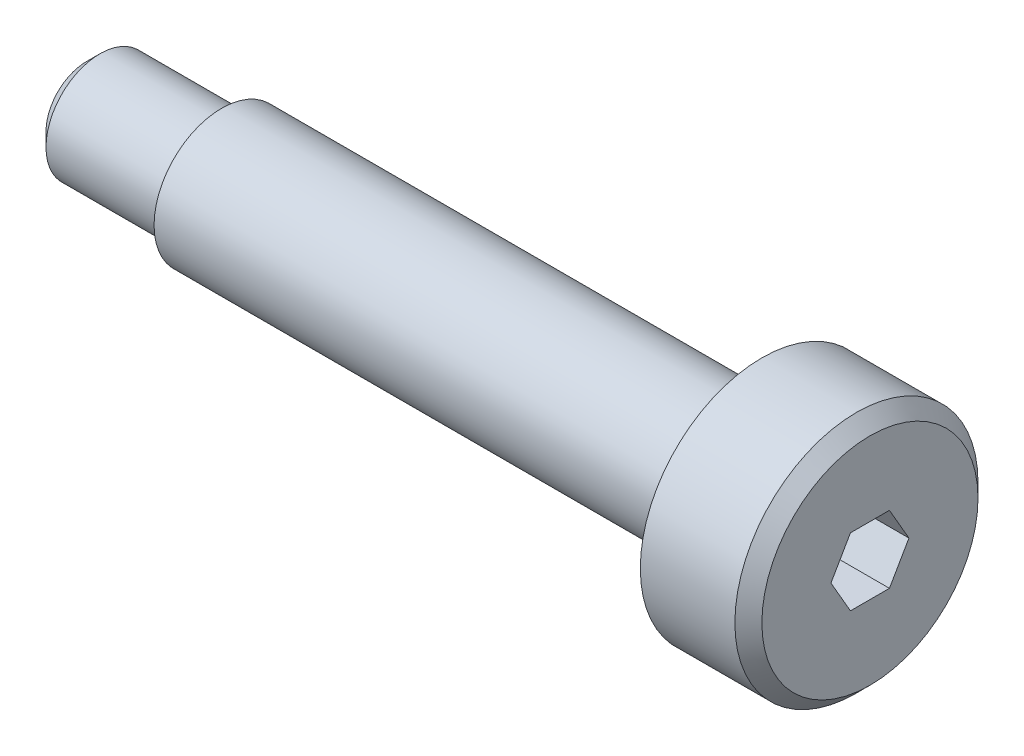
SolidWorks part; units mm, degrees
material "AISI Type 316L stainless steel"
ref_plane "Front Plane" through (0, 0, 0) normal (0, 0, 1) x (1, 0, 0)
ref_plane "Top Plane" through (0, 0, 0) normal (0, 1, 0) x (1, 0, 0)
ref_plane "Right Plane" through (0, 0, 0) normal (1, 0, 0) x (0, 0, -1)
sketch "Sketch1" plane through (0, 0, 0) normal (0, 0, 1) x (1, 0, 0)
  line L0 (0, 0) -> (29, 0)
  line L1 (29, 0) -> (29, 4)
  line L2 (28.5, 4.5) -> (25, 4.5)
  line L3 (25, 4.5) -> (25, 2.5)
  line L4 (25, 2.5) -> (5, 2.5)
  line L5 (5, 2.5) -> (5, 2)
  line L6 (5, 2) -> (0.5, 2)
  line L7 (0, 1.5) -> (0, 0)
  line L8 (0.5, 2) -> (0, 1.5)
  line L9 (29, 4) -> (28.5, 4.5)
  point P4 (29, 4.5)
  point P9 (0, 2)
  dimension "D1" = 20
  dimension "D2" = 2
  dimension "D3" = 5
  dimension "D4" = 2.5
  dimension "D5" = 4
  dimension "D6" = 4.5
revolve "Revolve1" add sketch "Sketch1" angle 360 about L0
sketch "Sketch2" plane through (29, 0, 0) normal (1, 0, 0) x (0, 0, -1)
  line L1 (1.4434, 0) -> (0.7217, 1.25)
  line L2 (0.7217, 1.25) -> (-0.7217, 1.25)
  line L3 (-0.7217, 1.25) -> (-1.4434, 0)
  line L4 (-1.4434, 0) -> (-0.7217, -1.25)
  line L5 (-0.7217, -1.25) -> (0.7217, -1.25)
  line L6 (0.7217, -1.25) -> (1.4434, 0)
  circle A0 centre (0, 0) radius 1.25 construction
  dimension "D1" = 2.5
extrude "Cut-Extrude1" cut sketch "Sketch2" against normal blind 4
